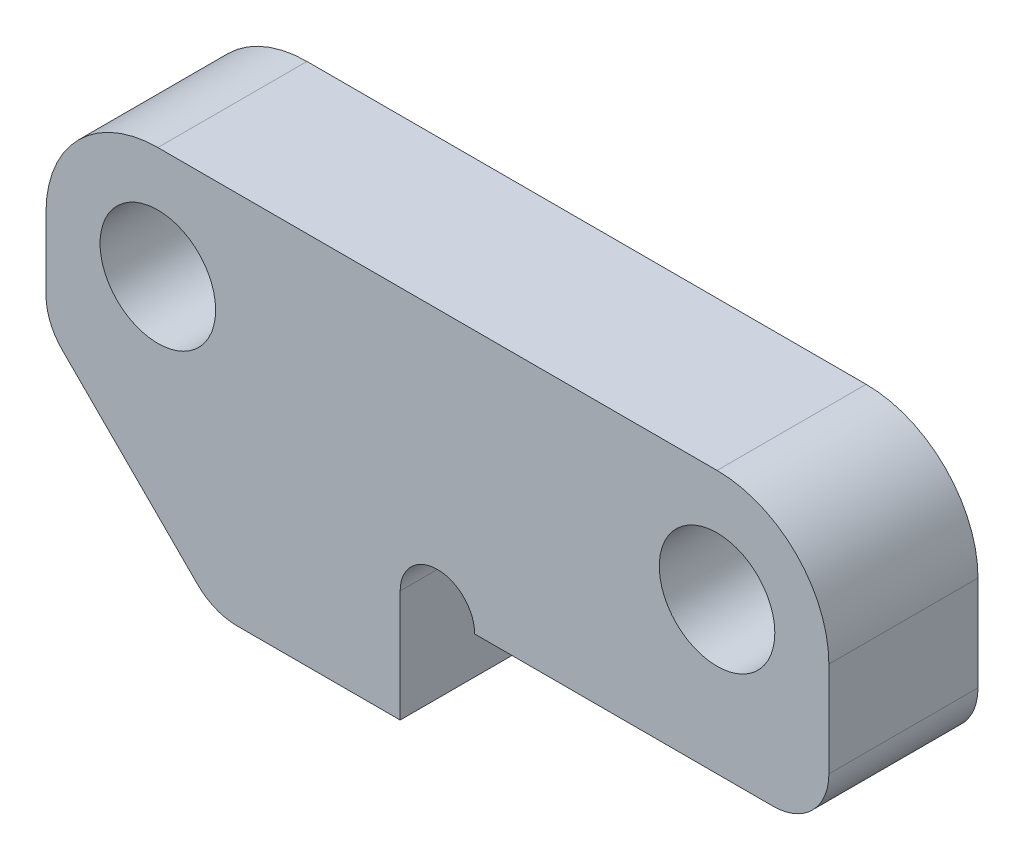
SolidWorks part; units mm, degrees
ref_plane "前视基准面" through (0, 0, 0) normal (0, 0, 1) x (1, 0, 0)
ref_plane "上视基准面" through (0, 0, 0) normal (0, 1, 0) x (1, 0, 0)
ref_plane "右视基准面" through (0, 0, 0) normal (1, 0, 0) x (0, 0, -1)
sketch "草图1" plane through (0, 0, 0) normal (0, 0, 1) x (1, 0, 0)
  line L0 (-10.5, 0) -> (10.5, 0)
  line L1 (10.5, 0) -> (10.5, -7.05)
  line L2 (10.5, -7.05) -> (-1, -7.05)
  line L3 (-1, -7.05) -> (-1, -10.05)
  line L4 (-1, -10.05) -> (-6, -10.05)
  line L5 (-6, -10.05) -> (-10.5, -5.55)
  line L6 (-10.5, -5.55) -> (-10.5, 0)
  line L7 (-7.5, -3) -> (7.5, -3) construction
  line L8 (-10.5, -11) -> (10.5, -11) construction
  circle A0 centre (-7.5, -3) radius 1.55
  circle A1 centre (7.5, -3) radius 1.55
  dimension "D2" = 3
  dimension "D3" = 3
  dimension "D5" = 3.1
  dimension "D1" = 11.5
  dimension "D4" = 3
  dimension "D6" = 15
  dimension "D7" = 3.95
  dimension "D8" = 8
  dimension "D9" = 3
  dimension "D10" = 45
  dimension "D11" = 4.5
extrude "凸台-拉伸1" add sketch "草图1" along normal mid plane 4
fillet "圆角1" radius 3 2 edges at (-10.5, 0, 0) (10.5, 0, 0)
fillet "圆角2" radius 1.5 3 edges at (10.5, -7.05, 0) (-6, -10.05, 0) (-10.5, -5.55, 0)
sketch "草图3" plane through (0, 0, 2) normal (0, 0, 1) x (1, 0, 0)
  line L0 (-1, -7.05) -> (9, -7.05) construction
  circle A0 centre (0, -7.05) radius 1
  dimension "D1" = 2
extrude "切除-拉伸1" cut sketch "草图3" against normal through all
